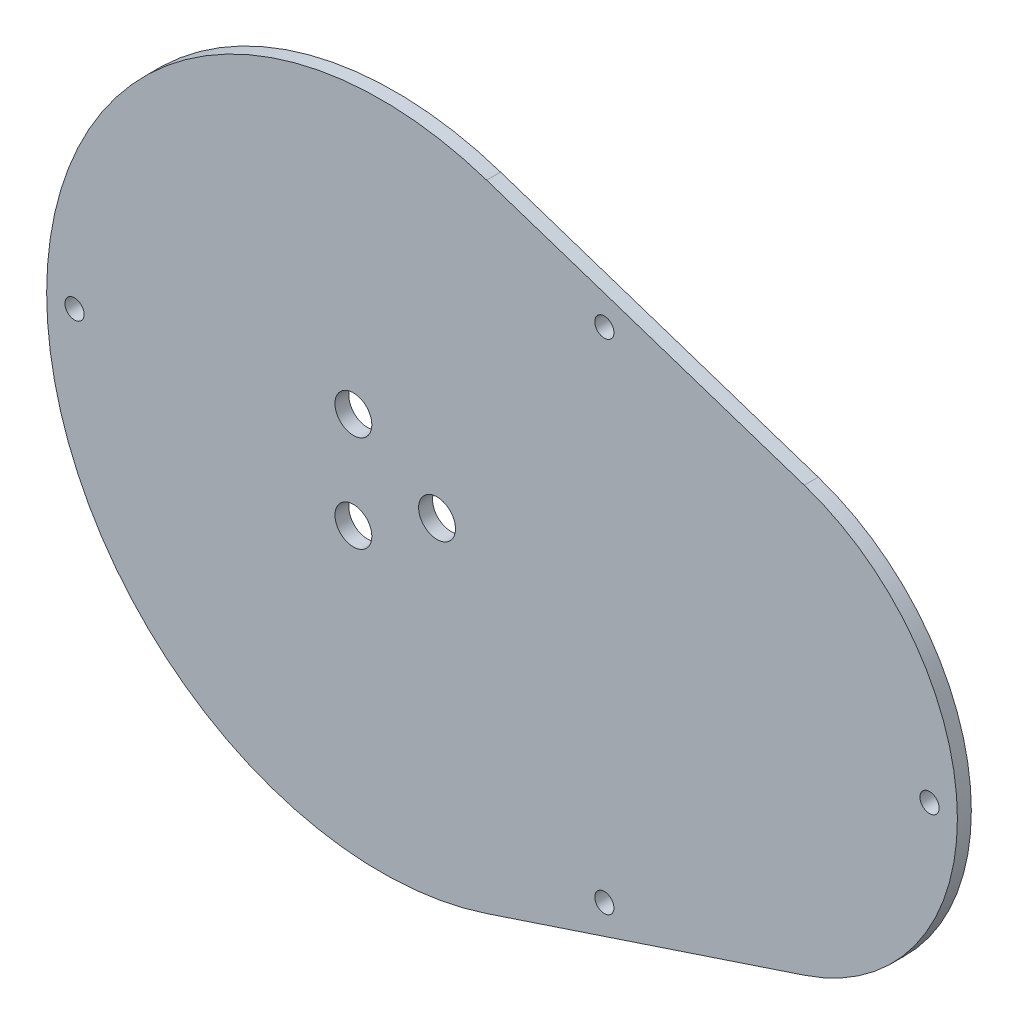
SolidWorks part; units mm, degrees
ref_plane "Front Plane" through (0, 0, 0) normal (0, 0, 1) x (1, 0, 0)
ref_plane "Top Plane" through (0, 0, 0) normal (0, 1, 0) x (1, 0, 0)
ref_plane "Right Plane" through (0, 0, 0) normal (1, 0, 0) x (0, 0, -1)
sketch "Sketch1" plane through (0, 0, 0) normal (0, 0, 1) x (1, 0, 0)
  line L0 (0, 0) -> (266.7, 0) construction
  line L1 (0, 0) -> (13.5739, -84.0003) construction
  line L2 (13.5739, -84.0003) -> (266.7, 0) construction
  line L3 (0, 0) -> (13.5739, 84.0003) construction
  line L4 (13.5739, 84.0003) -> (266.7, 0) construction
  line L5 (13.0001, 39.1743) -> (49.1609, 27.1742) construction
  line L6 (13.0001, -39.1743) -> (49.1609, -27.1742) construction
  line L7 (12, 36.1609) -> (48.1609, 24.1608)
  line L8 (12, -36.1609) -> (48.1609, -24.1608)
  arc A0 (13.0001, 39.1743) -> (13.0001, -39.1743) centre (0, 0) ccw construction
  arc A1 (49.1609, -27.1742) -> (49.1609, 27.1742) centre (40.1431, 0) ccw construction
  arc A2 (48.1609, -24.1608) -> (48.1609, 24.1608) centre (40.1431, 0) ccw
  arc A3 (12, 36.1609) -> (12, -36.1609) centre (0, 0) ccw
  circle A4 centre (62.4246, 0) radius 1.0922
  circle A5 centre (25.4, 28.3688) radius 1.0922
  circle A6 centre (25.4, -28.3688) radius 1.0922
  circle A7 centre (-34.925, 0) radius 1.0922
  circle A8 centre (0, 0) radius 6.35 construction
  circle A9 centre (6.35, 0) radius 2.1
  circle A10 centre (-3.175, -5.4993) radius 2.1
  circle A11 centre (-3.175, 5.4993) radius 2.1
  point P33 (0, 0)
  dimension "D2" = 82.55
  dimension "D7" = 2.1844
  dimension "D14" = 12.7
  dimension "D15" = 4.2
  dimension "D1" = 266.7
  dimension "D3" = 85.09
  dimension "D4" = 266.7
  dimension "D5" = 38.1
  dimension "D6" = 3.175
  dimension "D8" = 3.175
  dimension "D9" = 3.175
  dimension "D10" = 3.175
  dimension "D11" = 3.175
  dimension "D12" = 25.4
  dimension "D13" = 25.4
  dimension "D16" = 3
extrude "Boss-Extrude1" add sketch "Sketch1" along normal blind 1.5875
